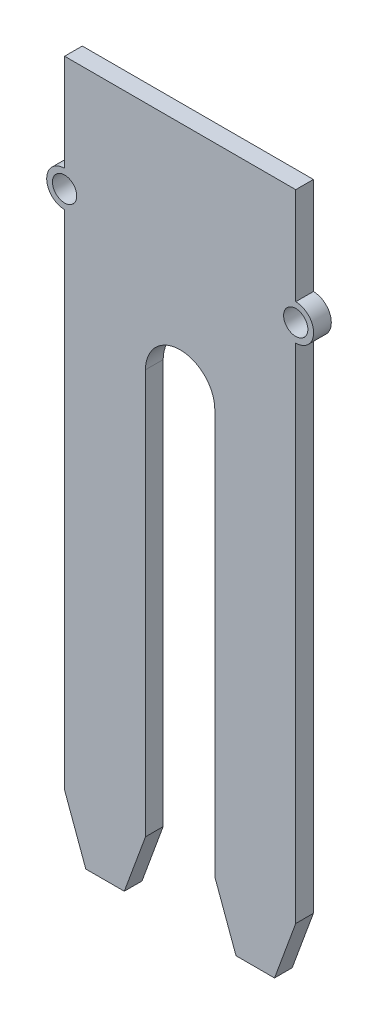
SolidWorks part; units mm, degrees
ref_plane "Plan de face" through (0, 0, 0) normal (0, 0, 1) x (1, 0, 0)
ref_plane "Plan de dessus" through (0, 0, 0) normal (0, 1, 0) x (1, 0, 0)
ref_plane "Plan de droite" through (0, 0, 0) normal (1, 0, 0) x (0, 0, -1)
sketch "Esquisse1" plane through (0, 0, 0) normal (0, 0, 1) x (1, 0, 0)
  line L0 (7.206, 60) -> (7.206, 40) construction
  line L1 (10.206, 5) -> (10.206, 40)
  line L2 (-2.794, 5) -> (-2.794, 48.5)
  line L3 (-2.794, 60) -> (17.206, 60)
  line L4 (17.206, 5) -> (17.206, 48.5)
  line L5 (4.206, 5) -> (4.206, 40)
  line L6 (-2.794, 5) -> (4.206, 5) construction
  line L7 (10.206, 5) -> (17.206, 5) construction
  line L8 (0.706, 5) -> (0.706, 0) construction
  line L9 (13.706, 5) -> (13.706, 0) construction
  line L10 (0.706, 0) -> (2.371, 0)
  line L11 (0.706, 0) -> (-0.959, 0)
  line L12 (13.706, 0) -> (12.041, 0)
  line L13 (13.706, 0) -> (15.371, 0)
  line L14 (2.371, 0) -> (4.206, 5)
  line L15 (-0.959, 0) -> (-2.794, 5)
  line L16 (12.041, 0) -> (10.206, 5)
  line L17 (15.371, 0) -> (17.206, 5)
  line L18 (-2.794, 51.6) -> (-2.794, 60)
  line L19 (17.206, 51.6) -> (17.206, 60)
  arc A0 (4.206, 40) -> (10.206, 40) centre (7.206, 40) cw
  circle A1 centre (17.206, 50.05) radius 1.05
  circle A2 centre (-2.794, 50.05) radius 1.05
  arc A3 (-2.794, 51.6) -> (-2.794, 48.5) centre (-2.794, 50.05) ccw
  arc A4 (17.206, 48.5) -> (17.206, 51.6) centre (17.206, 50.05) ccw
  dimension "D4" = 35
  dimension "D14" = 2.1
  dimension "D16" = 2.1
  dimension "D17" = 3.1
  dimension "D18" = 3.1
  dimension "D1" = 20
  dimension "D2" = 55
  dimension "D3" = 20
  dimension "D5" = 55
  dimension "D6" = 7
  dimension "D7" = 35
  dimension "D8" = 7
  dimension "D9" = 1.665
  dimension "D10" = 1.665
  dimension "D11" = 1.665
  dimension "D12" = 1.665
  dimension "D13" = 9.95
  dimension "D15" = 9.95
extrude "Boss.-Extru.1" add sketch "Esquisse1" along normal blind 1.53
